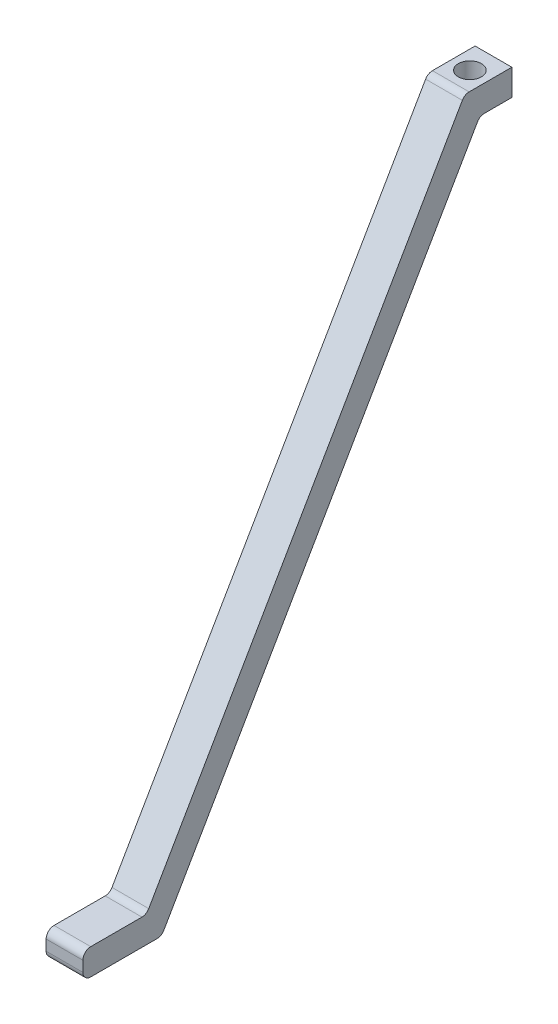
SolidWorks part; units mm, degrees
ref_plane "前视基准面" through (0, 0, 0) normal (0, 0, 1) x (1, 0, 0)
ref_plane "上视基准面" through (0, 0, 0) normal (0, 1, 0) x (1, 0, 0)
ref_plane "右视基准面" through (0, 0, 0) normal (1, 0, 0) x (0, 0, -1)
other "Configuration Table"
sketch "草图1" plane through (0, 0, 0) normal (0, 1, 0) x (1, 0, 0)
  line L1 (3.5, -4.5) -> (-3.5, -4.5)
  line L2 (3.5, -4.5) -> (3.5, 4.5)
  line L3 (3.5, 4.5) -> (-3.5, 4.5)
  line L4 (-3.5, -4.5) -> (-3.5, 4.5)
  line L5 (3.5, -4.5) -> (-3.5, 4.5) construction
  line L6 (3.5, 4.5) -> (-3.5, -4.5) construction
  point P0 (0, 0)
  point P6 (3.5, 0)
  dimension "D1" = 7
  dimension "D2" = 9
extrude "凸台-拉伸1" add sketch "草图1" along normal blind 10
sketch "草图2" plane through (0, 10, 0) normal (0, 1, 0) x (1, 0, 0)
  circle A0 centre (0, 0) radius 2.2
  dimension "D1" = 4.4
extrude "切除-拉伸1" cut sketch "草图2" against normal up to surface (10 mm away) up to face at (0, 0, 0)
sketch "草图3" plane through (-3.5, 0, 0) normal (-1, 0, 0) x (0, 0, 1)
  line L0 (4.5, 0) -> (62.235, -100)
  line L1 (4.5, 10) -> (65.1218, -95)
  line L2 (4.5, 0) -> (4.5, -100) construction
  line L3 (-4.5, 0) -> (4.5, 0) construction
  line L5 (4.5, -100) -> (20.9094, -100) construction
  line L7 (4.5, 10) -> (4.5, 0)
  line L8 (62.235, -100) -> (77.235, -100)
  line L9 (62.235, -100) -> (77.235, -100)
  line L11 (65.1218, -95) -> (77.235, -95)
  line L12 (77.235, -100) -> (77.235, -95)
  line L13 (62.235, -100) -> (77.235, -100)
  line M6 (4.5, 0) -> (4.5, 10)
  dimension "D1" = 120
  dimension "D2" = 110
  dimension "D3" = 5
  dimension "D4" = 15
extrude "凸台-拉伸2" add sketch "草图3" against normal up to surface (7 mm away) contours L8 L12 L11 L1 L0 M6 up to face at (3.5, 5, 0)
sketch "草图4" plane through (-3.5, 0, 0) normal (-1, 0, 0) x (0, 0, 1)
  line L0 (4.5, 0) -> (1.6132, 5)
  line L1 (1.6132, 5) -> (-4.5, 5)
  line L2 (-4.5, 10) -> (-4.5, 0) construction
  line L3 (-4.5, 5) -> (-4.5, 0)
  line L4 (-4.5, 0) -> (4.5, 0)
  line L5 (4.5, 0) -> (62.235, -100) construction
  line L6 (-4.5, 10) -> (4.5, 10) construction
  dimension "D1" = 5
extrude "切除-拉伸2" cut sketch "草图4" against normal up to surface (7 mm away) up to face at (3.5, -46.25, 35.2284)
fillet "圆角2" radius 1.5 1 edges at (0, 10, 4.5)
fillet "圆角3" radius 1.5 2 edges at (2.4979, 5, 1.6132) (-2.4979, 5, 1.6132)
fillet "圆角4" radius 1.5 4 edges at (0, -100, 77.235) (0, -95, 77.235) (0, -95, 65.1218) (0, -100, 62.235)
